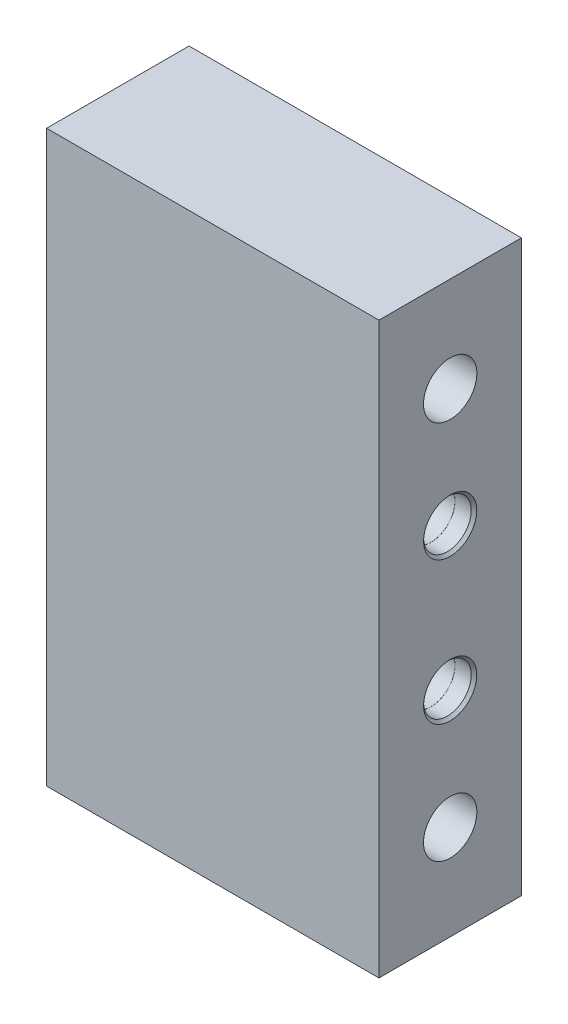
SolidWorks part; units mm, degrees
material "6061-T6 Al"
ref_plane "Front Plane" through (0, 0, 0) normal (0, 0, 1) x (1, 0, 0)
ref_plane "Top Plane" through (0, 0, 0) normal (0, 1, 0) x (1, 0, 0)
ref_plane "Right Plane" through (0, 0, 0) normal (1, 0, 0) x (0, 0, -1)
sketch "Sketch1" plane through (0, 0, 0) normal (0, 0, 1) x (1, 0, 0)
  line L0 (0, 0) -> (0, 38.1) construction
  line L1 (-22.225, 38.1) -> (22.225, 38.1)
  line L2 (-22.225, 38.1) -> (-22.225, -38.1)
  line L3 (-22.225, -38.1) -> (22.225, -38.1)
  line L4 (22.225, 38.1) -> (22.225, -38.1)
  dimension "D1" = 44.45
  dimension "D2" = 76.2
  dimension "D3" = 38.1
extrude "Extrude1" add sketch "Sketch1" along normal blind 19.05
hole_wizard "1/4 Clearance Hole1" positions "Sketch3" profile "Sketch2" hole size "1/4" standard "Ansi Inch" end condition through all
sketch "Sketch3" plane through (22.225, 0, 0) normal (1, 0, 0) x (0, 0, -1)
  line L0 (-19.05, 38.1) -> (0, 38.1) construction
  line L1 (-19.05, -38.1) -> (0, -38.1) construction
  line L2 (0, -38.1) -> (0, 38.1) construction
  point P0 (-9.525, 25.4)
  point P1 (-9.525, -25.4)
  dimension "D1" = 12.7
  dimension "D2" = 12.7
  dimension "D3" = 9.525
  dimension "D4" = 9.525
sketch "Sketch2" plane through (22.225, 25.4, 9.525) normal (0, 1, 0) x (0, 0, -1)
  line L0 (0, 0) -> (0, 44.45)
  line L1 (0, 44.45) -> (3.5712, 44.45)
  line L2 (3.5712, 44.45) -> (3.5712, 0)
  line L5 (3.5712, 0) -> (0, 0)
  line L11 (0, -6.35) -> (0, 107.95) construction
  dimension "Thru Hole Dia." = 7.1425
  dimension "Thru Hole Depth" = 44.45
hole_wizard "CBORE for 1/4 DOWEL" positions "Sketch5" profile "Sketch4" counterbore size "1/4" standard "Ansi Inch"
sketch "Sketch5" plane through (22.225, 0, 0) normal (1, 0, 0) x (0, 0, -1)
  line L0 (-19.05, -38.1) -> (-19.05, 38.1) construction
  line L1 (-19.05, 38.1) -> (0, 38.1) construction
  point P0 (-9.525, -9.525)
  point P1 (-9.525, 9.525)
  dimension "D1" = 19.05
  dimension "D2" = 28.575
  dimension "D3" = 9.525
  dimension "D4" = 9.525
sketch "Sketch4" plane through (22.225, -9.525, 9.525) normal (0, 1, 0) x (0, 0, -1)
  line L0 (0, 0) -> (0, 11.5597)
  line L1 (0, 11.5597) -> (3.175, 9.652)
  line L2 (3.175, 9.652) -> (3.175, 2.54)
  line L3 (3.175, 2.54) -> (3.1877, 2.54)
  line L5 (3.1877, 2.54) -> (3.1877, 0.3683)
  line L6 (3.1877, 0.3683) -> (3.556, 0)
  line L7 (3.556, 0) -> (0, 0)
  line L8 (-3.1877, 0.3683) -> (-3.556, 0) construction
  line L10 (0, 11.5597) -> (-3.175, 9.652) construction
  line L11 (0, -6.35) -> (0, 107.95) construction
  dimension "Hole Dia." = 6.35
  dimension "Hole Depth" = 9.652
  dimension "C'Bore Dia." = 6.3754
  dimension "C'Bore Depth" = 2.54
  dimension "Near C'Sink Dia." = 7.112
  dimension "Near C'Sink Angle" = 90
  dimension "Drill Angle" = 118
hole_wizard "3/16 (0.1875) Diameter Hole1" positions "Sketch7" profile "Sketch6" hole size "3/16" standard "Ansi Inch" end condition through all
sketch "Sketch7" plane through (22.225, 0, 0) normal (1, 0, 0) x (0, 0, -1)
  point P0 (-9.525, 9.525)
  point P1 (-9.525, -9.525)
sketch "Sketch6" plane through (22.225, 9.525, 9.525) normal (0, 1, 0) x (0, 0, -1)
  line L0 (0, 0) -> (0, 44.45)
  line L1 (0, 44.45) -> (2.3812, 44.45)
  line L2 (2.3812, 44.45) -> (2.3812, 0)
  line L5 (2.3812, 0) -> (0, 0)
  line L11 (0, -6.35) -> (0, 107.95) construction
  dimension "Thru Hole Dia." = 4.7625
  dimension "Thru Hole Depth" = 44.45
mirror "Mirror1" about plane through (0, 0, 0) normal (1, 0, 0) of "CBORE for 1/4 DOWEL"
